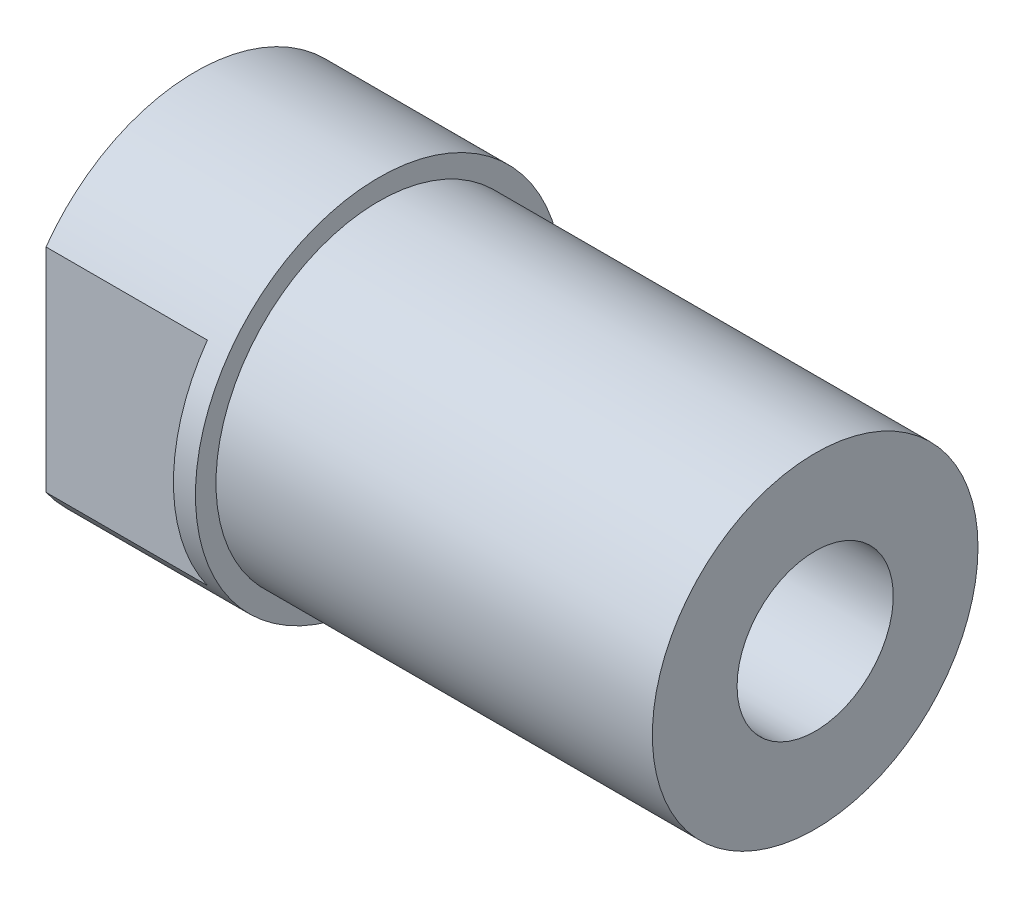
SolidWorks part; units mm, degrees
material "AISI 4130 Steel, normalized at 870C"
ref_plane "Top" through (0, 0, 0) normal (0, 0, 1) x (1, 0, 0)
ref_plane "Right" through (0, 0, 0) normal (0, 1, 0) x (1, 0, 0)
ref_plane "Front" through (0, 0, 0) normal (1, 0, 0) x (0, 0, -1)
sketch "Sketch2" plane through (0, 0, 0) normal (1, 0, 0) x (0, 0, -1)
  circle A0 centre (0, 0) radius 6.35
  dimension "D1" = 12.7
extrude "Boss-Extrude1" add sketch "Sketch2" against normal blind 6.35
sketch "Sketch3" plane through (0, 0, 0) normal (1, 0, 0) x (0, 0, -1)
  circle A0 centre (0, 0) radius 5.6388
  circle A1 centre (0, 0) radius 6.35 construction
  dimension "D1" = 0.7112
extrude "Boss-Extrude2" add sketch "Sketch3" along normal blind 15.113
sketch "Sketch4" plane through (0, 0, 0) normal (0, 1, 0) x (1, 0, 0)
  line L1 (-6.35, 6.35) -> (-0.762, 6.35)
  line L2 (-6.35, 6.35) -> (-6.35, 5.1752)
  line L3 (-6.35, 5.1752) -> (-0.762, 5.1752)
  line L4 (-0.762, 6.35) -> (-0.762, 5.1752)
  line L5 (-6.35, -6.35) -> (-0.762, -6.35)
  line L6 (-6.35, -6.35) -> (-6.35, -5.1752)
  line L7 (-6.35, -5.1752) -> (-0.762, -5.1752)
  line L8 (-0.762, -6.35) -> (-0.762, -5.1752)
  dimension "D1" = 10.3505
  dimension "D2" = 5.588
extrude "Cut-Extrude1" cut sketch "Sketch4" against normal mid plane 12.7
hole_wizard "1/4-28 Tapped Hole1" positions "3DSketch1" profile "Sketch5" tap size "1/4-28" standard "ANSI Inch" end condition through all
sketch3d "3DSketch1"
  arc A0 (-6.35, -3.6796, 5.1752) -> (-6.35, -3.6796, -5.1752) centre (-6.35, 0, 0) ccw construction
  arc A1 (-6.35, -3.6796, 5.1752) -> (-6.35, -3.6796, -5.1752) centre (-6.35, 0, 0) ccw
  point P1 (-6.35, 0, 0)
  point P4 (0, 0, 0)
  point P5 (0, 0, 0)
  point P9 (-6.35, 0, 0)
  point P12 (-6.35, 0, 0)
sketch "Sketch5" plane through (-6.35, 0, 0) normal (0, 1, 0) x (0, 0, 1)
  line L0 (0, 0) -> (0, 21.463)
  line L1 (0, 21.463) -> (2.7051, 21.463)
  line L2 (2.7051, 21.463) -> (2.7051, 0)
  line L5 (2.7051, 0) -> (0, 0)
  line L11 (0, -6.35) -> (0, 107.95) construction
  dimension "Thru Tap Drill Dia." = 5.4102
  dimension "Thru Tap Drill Depth" = 21.463
cosmetic thread "Hole Thread7" parameters "D2"=6.35
hole_wizard "5/16-24 Tapped Hole1" [suppressed] positions "3DSketch2" profile "Sketch6" tap size "5/16-24" standard "ANSI Inch"
sketch3d "3DSketch2"
  arc A0 (-6.35, -3.6796, 5.1752) -> (-6.35, -3.6796, -5.1752) centre (-6.35, 0, 0) ccw construction
  arc A1 (-6.35, -3.6796, 5.1752) -> (-6.35, -3.6796, -5.1752) centre (-6.35, 0, 0) ccw
  point P0 (-6.35, 0, 0)
  point P6 (0, 0, 0)
  point P7 (0, 0, 0)
sketch "Sketch6" plane through (-6.35, 0, 0) normal (0, 1, 0) x (0, 0, 1)
  line L0 (0, 0) -> (0, 21.463)
  line L1 (0, 21.463) -> (3.4544, 21.463)
  line L2 (3.4544, 21.463) -> (3.4544, 0)
  line L5 (3.4544, 0) -> (0, 0)
  line L11 (0, -6.35) -> (0, 107.95) construction
  dimension "Thru Tap Drill Dia." = 6.9088
  dimension "Thru Tap Drill Depth" = 21.463
cosmetic thread "Hole Thread8" [suppressed] parameters "D2"=7.9375
hole_wizard "M6x1.0 Tapped Hole2" [suppressed] positions "Sketch9" profile "Sketch10" tap size "M6x1.0" standard "ANSI Metric"
sketch "Sketch9" plane through (-6.35, 0, 0) normal (-1, 0, 0) x (0, 0, 1)
  point P0 (0, 0)
sketch "Sketch10" plane through (-6.35, 0, 0) normal (0, 1, 0) x (0, 0, 1)
  line L0 (0, 0) -> (0, 21.463)
  line L1 (0, 21.463) -> (2.5, 21.463)
  line L2 (2.5, 21.463) -> (2.5, 0)
  line L5 (2.5, 0) -> (0, 0)
  line L11 (0, -6.35) -> (0, 107.95) construction
  dimension "Thru Tap Drill Dia." = 5
  dimension "Thru Tap Drill Depth" = 21.463
equation "\"OD\"= 0.5"
equation "\"Wall\"= 0.028"
